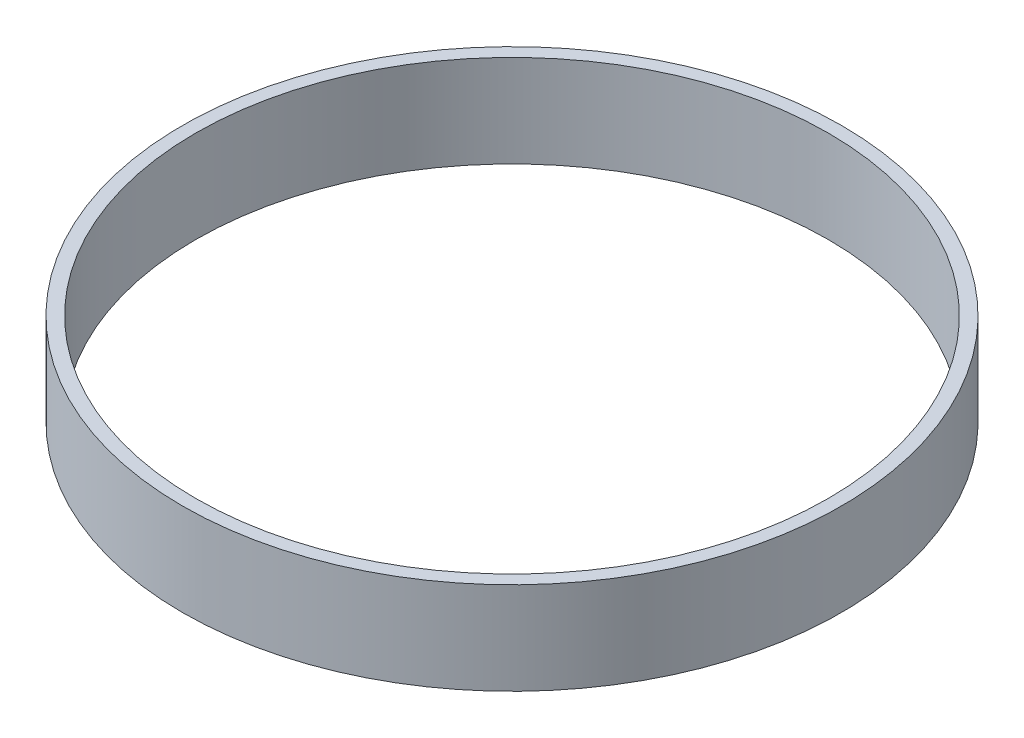
SolidWorks part; units mm, degrees
material "Acrylic (Medium-high impact)"
ref_plane "Front Plane" through (0, 0, 0) normal (0, 0, 1) x (1, 0, 0)
ref_plane "Top Plane" through (0, 0, 0) normal (0, 1, 0) x (1, 0, 0)
ref_plane "Right Plane" through (0, 0, 0) normal (1, 0, 0) x (0, 0, -1)
sketch "Sketch1" plane through (0, 0, 0) normal (0, 1, 0) x (1, 0, 0)
  circle A0 centre (0, 0) radius 75
  circle A1 centre (0, 0) radius 72
  dimension "D1" = 3
  dimension "D2" = 150
extrude "Boss-Extrude1" add sketch "Sketch1" along normal blind 21
